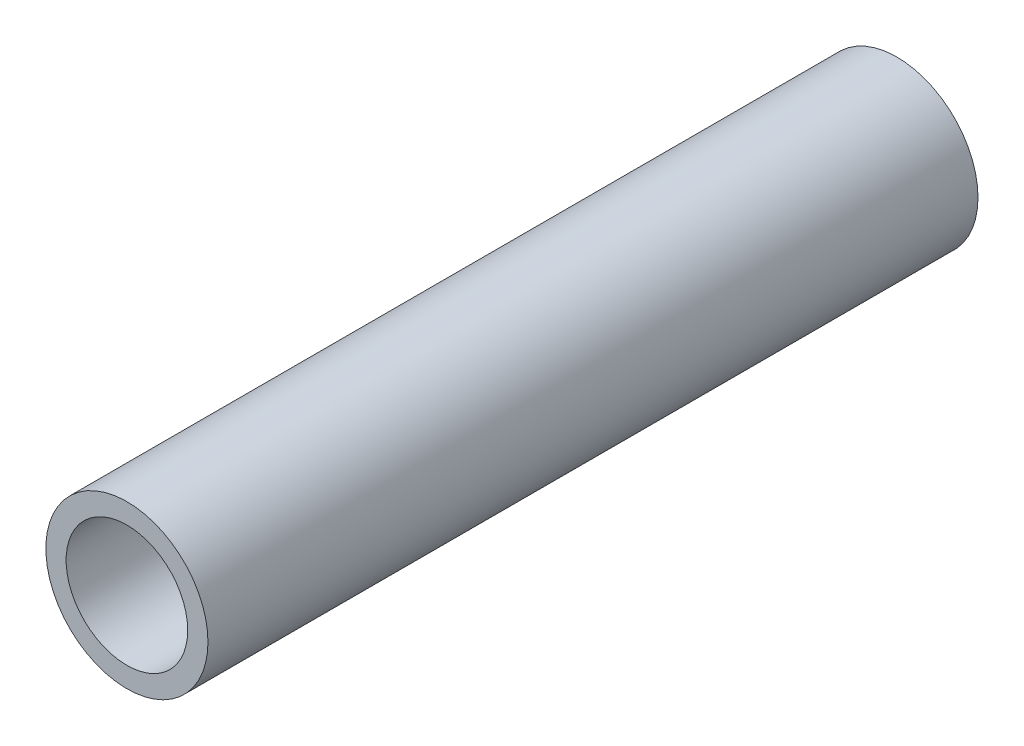
SolidWorks part; units mm, degrees
ref_plane "Alzado" through (0, 0, 0) normal (0, 0, 1) x (1, 0, 0)
ref_plane "Planta" through (0, 0, 0) normal (0, 1, 0) x (1, 0, 0)
ref_plane "Vista lateral" through (0, 0, 0) normal (1, 0, 0) x (0, 0, -1)
sketch "Croquis1" plane through (0, 0, 0) normal (0, 0, 1) x (1, 0, 0)
  circle A0 centre (0, 0) radius 4
  circle A1 centre (0, 0) radius 3
  dimension "D1" = 8
  dimension "D2" = 1
extrude "Saliente-Extruir1" add sketch "Croquis1" along normal blind 38
